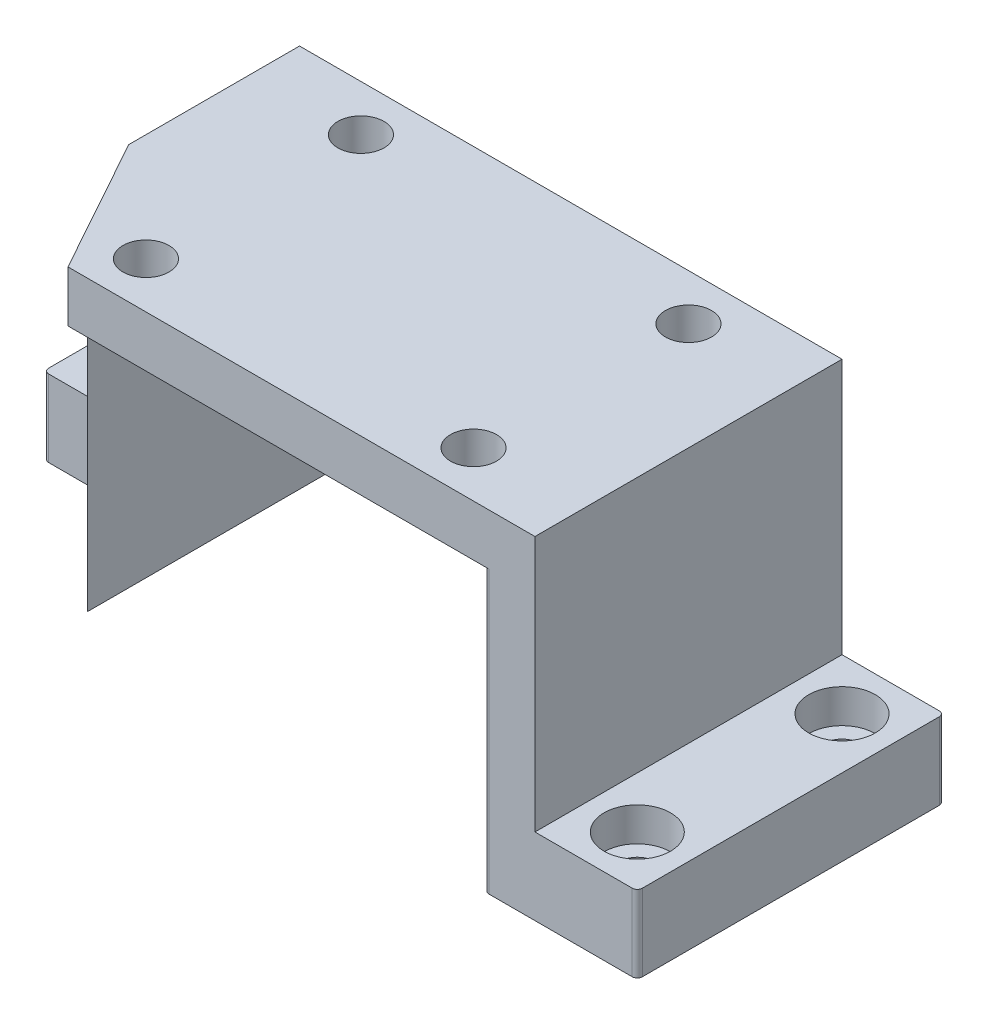
SolidWorks part; units mm, degrees
material "3003 Alloy"
ref_plane "Front Plane" through (0, 0, 0) normal (0, 0, 1) x (1, 0, 0)
ref_plane "Top Plane" through (0, 0, 0) normal (0, 1, 0) x (1, 0, 0)
ref_plane "Right Plane" through (0, 0, 0) normal (1, 0, 0) x (0, 0, -1)
sketch "Sketch1" plane through (0, 0, 0) normal (0, 1, 0) x (1, 0, 0)
  line L1 (-53, -30) -> (53, -30)
  line L2 (-53, -30) -> (-53, 30)
  line L3 (-53, 30) -> (53, 30)
  line L4 (53, -30) -> (53, 30)
  line L5 (-53, -30) -> (53, 30) construction
  line L6 (-53, 30) -> (53, -30) construction
  point P0 (0, 0)
  dimension "D1" = 60
  dimension "D2" = 106
extrude "Boss-Extrude1" add sketch "Sketch1" along normal blind 10
sketch "Sketch2" plane through (0, 0, 0) normal (0, -1, 0) x (1, 0, 0)
  line L0 (53, -30) -> (-53, -30) construction
  line L1 (-53, 30) -> (-43, 30)
  line L2 (-53, 30) -> (-53, -30)
  line L3 (-53, -30) -> (-43, -30)
  line L4 (-43, 30) -> (-43, -30)
  line L6 (53, 30) -> (43, 30)
  line L7 (53, 30) -> (53, -30)
  line L8 (53, -30) -> (43, -30)
  line L9 (43, 30) -> (43, -30)
  dimension "D1" = 10
  dimension "D2" = 10
extrude "Boss-Extrude2" add sketch "Sketch2" along normal blind 55
sketch "Sketch3" plane through (53, 0, 0) normal (1, 0, 0) x (0, 0, -1)
  line L0 (30, 10) -> (30, -55) construction
  line L1 (-30, -55) -> (30, -55)
  line L2 (-30, -55) -> (-30, -40)
  line L3 (-30, -40) -> (30, -40)
  line L4 (30, -55) -> (30, -40)
  dimension "D1" = 15
extrude "Boss-Extrude3" add sketch "Sketch3" along normal blind 20
sketch "Sketch4" plane through (-53, 0, 0) normal (-1, 0, 0) x (0, 0, 1)
  line L1 (-30, -55) -> (0, -55)
  line L2 (-30, -55) -> (-30, -40)
  line L3 (-30, -40) -> (0, -40)
  line L5 (0, -40) -> (0, -55)
  dimension "D1" = 15
  dimension "D2" = 30
extrude "Boss-Extrude4" add sketch "Sketch4" along normal blind 20
sketch "Sketch5" plane through (0, 10, 0) normal (0, 1, 0) x (1, 0, 0)
  line L0 (0, 0) -> (0, 30) construction
  line L1 (53, 30) -> (-53, 30) construction
  line L2 (0, 0) -> (18.8591, 0) construction
  circle A0 centre (-32, 21) radius 4.5
  circle A1 centre (32, 21) radius 4.5
  circle A2 centre (32, -21) radius 4.5
  circle A3 centre (-32, -21) radius 4.5
  dimension "D3" = 9
  dimension "D1" = 32
  dimension "D2" = 21
extrude "Cut-Extrude1" cut sketch "Sketch5" against normal through all
sketch "Sketch6" plane through (0, -40, 0) normal (0, 1, 0) x (1, 0, 0)
  line L0 (73, 30) -> (53, 30) construction
  line L1 (73, 30) -> (73, -30) construction
  line L2 (73, -30) -> (53, -30) construction
  line L3 (-73, 0) -> (-73, 30) construction
  line L4 (-73, 30) -> (-53, 30) construction
  circle A0 centre (63, 20) radius 6.5
  circle A1 centre (63, -20) radius 6.5
  circle A2 centre (-63, 20) radius 6.5
  dimension "D2" = 10
  dimension "D10" = 13
  dimension "D11" = 13
  dimension "D12" = 13
  dimension "D1" = 10
  dimension "D3" = 10
  dimension "D4" = 10
  dimension "D5" = 10
  dimension "D6" = 10
extrude "Cut-Extrude2" cut sketch "Sketch6" against normal blind 6.6
sketch "Sketch7" plane through (0, -46.6, 0) normal (0, 1, 0) x (1, 0, 0)
  circle A0 centre (-63, 20) radius 3.3
  circle A2 centre (63, -20) radius 3.3
  circle A3 centre (63, 20) radius 3.3
  dimension "D1" = 6.6
  dimension "D3" = 6.6
  dimension "D4" = 6.6
extrude "Cut-Extrude3" cut sketch "Sketch7" against normal through all
sketch "Sketch8" plane through (0, 10, 0) normal (0, 1, 0) x (1, 0, 0)
  line L0 (-53, -30) -> (53, -30) construction
  line L1 (53, 30) -> (53, -30) construction
  line L2 (-38.239, -30) -> (-53, -3.3705)
  line L3 (-53, 30) -> (-53, -30) construction
  line L4 (-53, -3.3705) -> (-53, -30)
  line L5 (-53, -30) -> (-38.239, -30)
  point P0 (-38.239, -30)
  dimension "D1" = 91.239
  dimension "D2" = 119
extrude "Cut-Extrude4" cut sketch "Sketch8" against normal through all
fillet "Fillet1" radius 1 7 edges at (-43, -27.5, -30) (-73, -47.5, 0) (-73, -47.5, -30) (73, -47.5, -30) (43, -27.5, -30) (43, -27.5, 30) (73, -47.5, 30)
